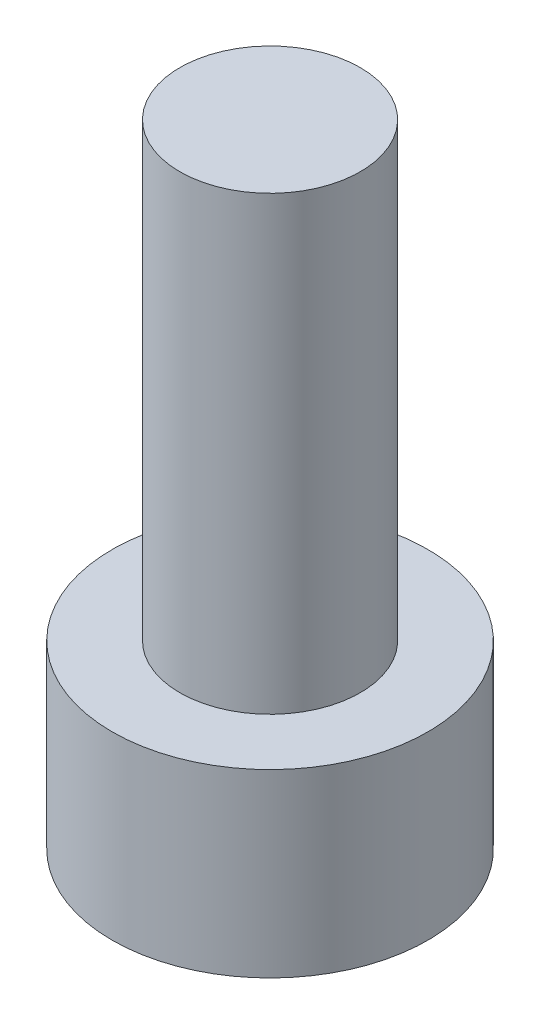
SolidWorks part; units mm, degrees
ref_plane "Front Plane" through (0, 0, 0) normal (0, 0, 1) x (1, 0, 0)
ref_plane "Top Plane" through (0, 0, 0) normal (0, 1, 0) x (1, 0, 0)
ref_plane "Right Plane" through (0, 0, 0) normal (1, 0, 0) x (0, 0, -1)
sketch "Sketch1" plane through (0, 0, 0) normal (0, 1, 0) x (1, 0, 0)
  circle A0 centre (0, 0) radius 3.5
  dimension "D1" = 7
extrude "Boss-Extrude1" add sketch "Sketch1" along normal blind 4
sketch "Sketch2" plane through (0, 4, 0) normal (0, 1, 0) x (1, 0, 0)
  circle A0 centre (0, 0) radius 2
  dimension "D1" = 4
extrude "Boss-Extrude2" add sketch "Sketch2" along normal blind 10
